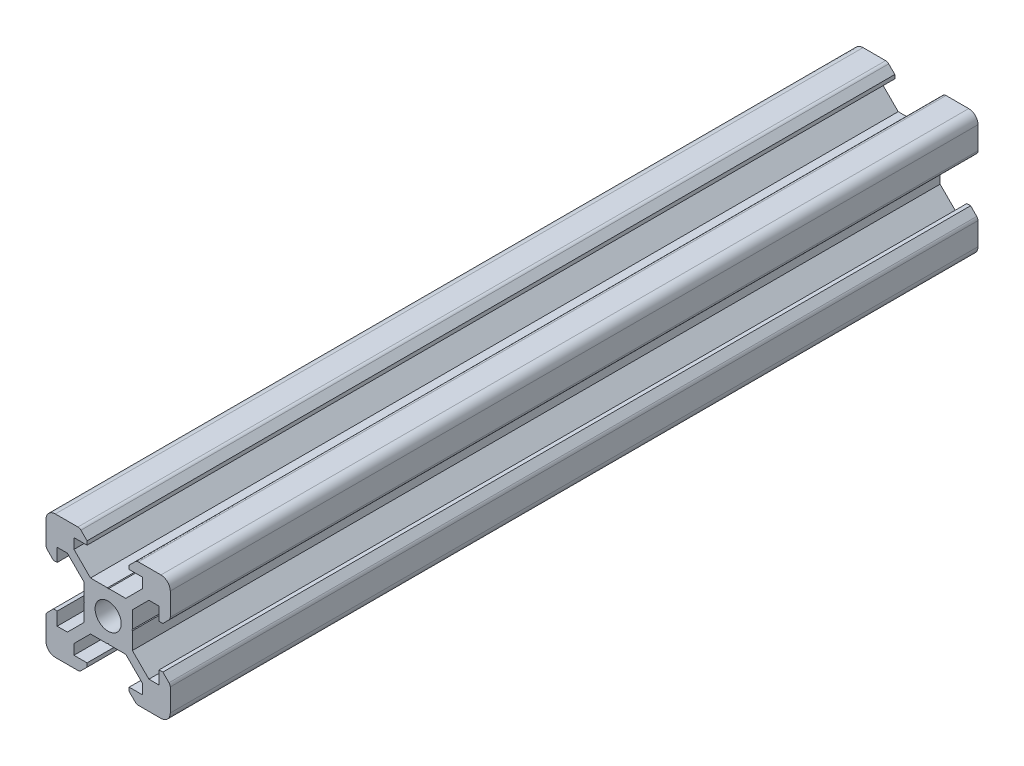
SolidWorks part; units mm, degrees
ref_plane "Front" through (0, 0, 0) normal (0, 0, 1) x (1, 0, 0)
ref_plane "Top" through (0, 0, 0) normal (0, 1, 0) x (1, 0, 0)
ref_plane "Right" through (0, 0, 0) normal (1, 0, 0) x (0, 0, -1)
sketch "Sketch1" plane through (0, 0, 0) normal (0, 0, 1) x (1, 0, 0)
  line L0 (-8.5, 10) -> (-10, 8.5) construction
  line L1 (-8.5, 10) -> (-4.8628, 10)
  line L2 (-10, 8.5) -> (-10, 4.8628)
  line L3 (-8.5, -10) -> (-4.8628, -10)
  line L4 (10, 8.5) -> (10, 4.8628)
  line L5 (-10, 10) -> (10, -10) construction
  line L6 (-10, -10) -> (10, 10) construction
  line L7 (-5.5, -8.2) -> (-3.3865, -8.2)
  line L8 (-8.2, -5.5) -> (-8.2, -3.3865)
  line L9 (-5.5, 8.2) -> (-3.3865, 8.2)
  line L10 (8.2, -5.5) -> (8.2, -3.3865)
  line L11 (-3.9005, 2.8395) -> (-6.561, 5.5)
  line L12 (-6.561, 5.5) -> (-8.2, 5.5)
  line L13 (-2.8395, -3.9005) -> (-0.1, -3.9005)
  line L14 (-3.9005, -2.8395) -> (-3.9005, -0.1)
  line L15 (-2.8395, 3.9005) -> (-0.1, 3.9005)
  line L16 (3.9005, -2.8395) -> (3.9005, -0.1)
  line L17 (-8.2, 3.3865) -> (-8.81, 3.3865)
  line L18 (-8.81, 3.3865) -> (-9.7976, 4.3741)
  line L19 (8.5, 10) -> (10, 8.5) construction
  line L20 (-2.8395, 3.9005) -> (-5.5, 6.561)
  line L21 (-5.5, 6.561) -> (-5.5, 8.2)
  line L22 (-3.3865, 8.2) -> (-3.3865, 8.81)
  line L23 (-3.3865, 8.81) -> (-4.3741, 9.7976)
  line L24 (0, 24.069) -> (0, -33.8154) construction
  line L25 (3.3865, 8.81) -> (4.3741, 9.7976)
  line L26 (3.3865, 8.2) -> (3.3865, 8.81)
  line L27 (5.5, 6.561) -> (5.5, 8.2)
  line L28 (2.8395, 3.9005) -> (5.5, 6.561)
  line L29 (3.3865, 8.2) -> (5.5, 8.2)
  line L30 (4.8628, 10) -> (8.5, 10)
  line L31 (-0.1, 3.9005) -> (0, 3.8005)
  line L32 (0.1, 3.9005) -> (0, 3.8005)
  line L33 (0.1, 3.9005) -> (2.8395, 3.9005)
  line L34 (25.9287, 0) -> (-28.3459, 0) construction
  line L35 (-0.1, -3.9005) -> (0, -3.8005)
  line L36 (0.1, -3.9005) -> (0, -3.8005)
  line L37 (0.1, -3.9005) -> (2.8395, -3.9005)
  line L38 (-3.9005, 0.1) -> (-3.8005, 0)
  line L39 (-3.8005, 0) -> (-3.9005, -0.1)
  line L40 (-3.9005, 0.1) -> (-3.9005, 2.8395)
  line L41 (3.9005, 0.1) -> (3.8005, 0)
  line L42 (3.8005, 0) -> (3.9005, -0.1)
  line L43 (3.9005, 0.1) -> (3.9005, 2.8395)
  line L44 (8.81, 3.3865) -> (9.7976, 4.3741)
  line L45 (8.2, 3.3865) -> (8.81, 3.3865)
  line L46 (6.561, 5.5) -> (8.2, 5.5)
  line L47 (3.9005, 2.8395) -> (6.561, 5.5)
  line L48 (2.8395, -3.9005) -> (5.5, -6.561)
  line L49 (3.9005, -2.8395) -> (6.561, -5.5)
  line L50 (-2.8395, -3.9005) -> (-5.5, -6.561)
  line L51 (-3.9005, -2.8395) -> (-6.561, -5.5)
  line L52 (6.561, -5.5) -> (8.2, -5.5)
  line L53 (-6.561, -5.5) -> (-8.2, -5.5)
  line L54 (-8.81, -3.3865) -> (-9.7976, -4.3741)
  line L55 (-8.2, -3.3865) -> (-8.81, -3.3865)
  line L56 (8.81, -3.3865) -> (9.7976, -4.3741)
  line L57 (8.2, -3.3865) -> (8.81, -3.3865)
  line L58 (8.2, 3.3865) -> (8.2, 5.5)
  line L59 (10, -4.8628) -> (10, -8.5)
  line L60 (-8.2, 3.3865) -> (-8.2, 5.5)
  line L61 (-10, -4.8628) -> (-10, -8.5)
  line L62 (-3.3865, -8.81) -> (-4.3741, -9.7976)
  line L63 (-3.3865, -8.2) -> (-3.3865, -8.81)
  line L64 (3.3865, -8.81) -> (4.3741, -9.7976)
  line L65 (3.3865, -8.2) -> (3.3865, -8.81)
  line L66 (-5.5, -6.561) -> (-5.5, -8.2)
  line L67 (5.5, -6.561) -> (5.5, -8.2)
  line L68 (3.3865, -8.2) -> (5.5, -8.2)
  line L69 (4.8628, -10) -> (8.5, -10)
  circle A0 centre (0, 0) radius 2.1
  arc A1 (-8.5, 10) -> (-10, 8.5) centre (-8.5, 8.5) ccw
  arc A2 (10, 8.5) -> (8.5, 10) centre (8.5, 8.5) ccw
  arc A3 (-4.3741, 9.7976) -> (-4.8628, 10) centre (-4.8628, 9.3088) ccw
  arc A4 (4.8628, 10) -> (4.3741, 9.7976) centre (4.8628, 9.3088) ccw
  arc A5 (-8.5, -10) -> (-10, -8.5) centre (-8.5, -8.5) cw
  arc A6 (9.7976, 4.3741) -> (10, 4.8628) centre (9.3088, 4.8628) ccw
  arc A7 (-10, 4.8628) -> (-9.7976, 4.3741) centre (-9.3088, 4.8628) ccw
  arc A8 (-10, -4.8628) -> (-9.7976, -4.3741) centre (-9.3088, -4.8628) cw
  arc A9 (9.7976, -4.3741) -> (10, -4.8628) centre (9.3088, -4.8628) cw
  arc A10 (10, -8.5) -> (8.5, -10) centre (8.5, -8.5) cw
  arc A11 (-4.3741, -9.7976) -> (-4.8628, -10) centre (-4.8628, -9.3088) cw
  arc A12 (4.8628, -10) -> (4.3741, -9.7976) centre (4.8628, -9.3088) cw
  point P17 (-9.25, 9.25)
  point P21 (9.25, 9.25)
  dimension "D2" = 4.2
  dimension "D4" = 1.5
  dimension "D3" = 20
  dimension "D5" = 0.529
  dimension "D6" = 6.773
  dimension "D7" = 90
  dimension "D8" = 11
  dimension "D9" = 0.61
  dimension "D10" = 0.1
  dimension "D11" = 0.1
  dimension "D12" = 0.1
  dimension "D13" = 0.1
  dimension "D14" = 5.679
  dimension "D15" = 1.639
  dimension "D16" = 1.8
  dimension "D17" = 90
  dimension "D18" = 6.773
  dimension "D19" = 90
extrude "Boss-Extrude1" add sketch "Sketch1" along normal blind 130
